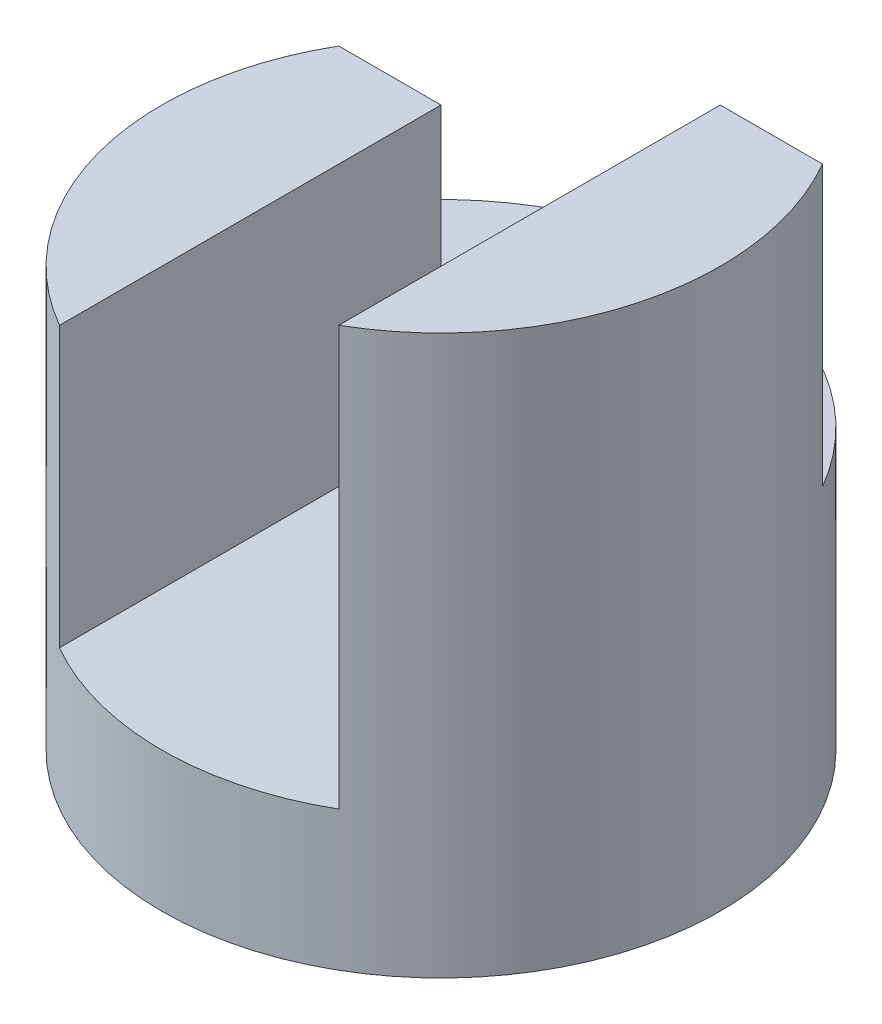
SolidWorks part; units mm, degrees
ref_plane "Front" through (0, 0, 0) normal (0, 0, 1) x (1, 0, 0)
ref_plane "Top" through (0, 0, 0) normal (0, 1, 0) x (1, 0, 0)
ref_plane "Right" through (0, 0, 0) normal (1, 0, 0) x (0, 0, -1)
sketch "Sketch1" plane through (0, 0, 0) normal (0, 1, 0) x (1, 0, 0)
  circle A0 centre (0, 0) radius 2
  dimension "D1" = 4
extrude "Boss-Extrude1" add sketch "Sketch1" along normal blind 4
sketch "Sketch3" plane through (0, 4, 0) normal (0, 1, 0) x (1, 0, 0)
  line L0 (-1.7321, 1) -> (1.7321, 1)
  arc A0 (-1.7321, 1) -> (1.7321, 1) centre (0, 0) cw
extrude "Cut-Extrude2" cut sketch "Sketch3" against normal blind 2
sketch "Sketch4" plane through (0, 0, 0) normal (0, 0, 1) x (1, 0, 0)
  line L0 (-2, 3) -> (-1, 3)
  line L1 (-2, 4) -> (-2, 0) construction
  line L2 (-1, 3) -> (-1, 2)
  line L3 (-1, 2) -> (1, 2)
  line L4 (1, 2) -> (1, 4)
  line L5 (2, 4) -> (-2, 4) construction
  line L6 (1, 4) -> (-2, 4)
  line L7 (-2, 4) -> (-2, 3)
  line L8 (2, 0) -> (2, 4) construction
  dimension "D1" = 1
  dimension "D2" = 1
  dimension "D3" = 2
  dimension "D4" = 1
extrude "Cut-Extrude3" cut sketch "Sketch4" against normal mid plane 11
sketch "Sketch5" plane through (0, 2, 0) normal (0, 1, 0) x (1, 0, 0)
  line L1 (1, 1) -> (-1, 1)
  line L2 (1, 1) -> (1, -2.0906)
  line L3 (1, -2.0906) -> (-1, -2.0906)
  line L4 (-1, 1) -> (-1, -2.0906)
  dimension "D1" = 2
extrude "Cut-Extrude4" cut sketch "Sketch5" against normal blind 1
